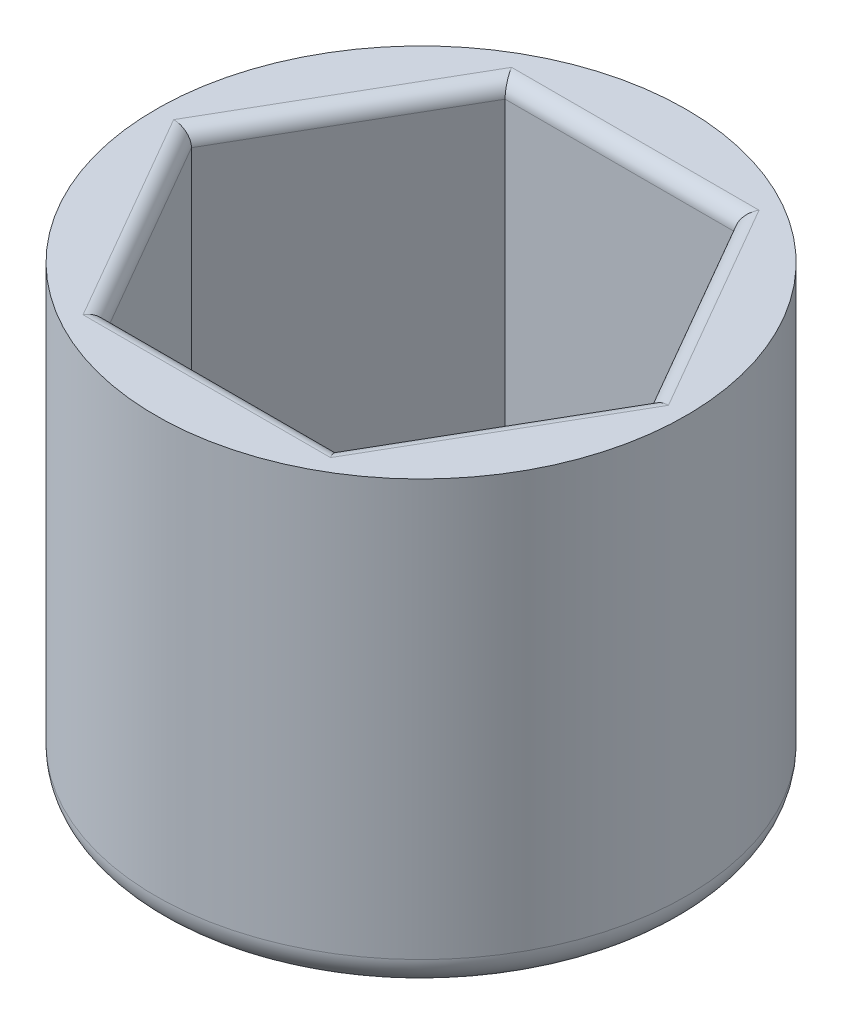
SolidWorks part; units mm, degrees
ref_plane "Alzado" through (0, 0, 0) normal (0, 0, 1) x (1, 0, 0)
ref_plane "Planta" through (0, 0, 0) normal (0, 1, 0) x (1, 0, 0)
ref_plane "Vista lateral" through (0, 0, 0) normal (1, 0, 0) x (0, 0, -1)
sketch "Croquis1" plane through (0, 0, 0) normal (0, 1, 0) x (1, 0, 0)
  line L0 (8.6025, 0) -> (4.3013, 7.45)
  line L1 (-3.7239, 6.45) -> (-7.4478, 0)
  line L2 (-7.4478, 0) -> (-3.7239, -6.45)
  line L3 (-3.7239, -6.45) -> (3.7239, -6.45)
  line L4 (3.7239, -6.45) -> (7.4478, 0)
  line L5 (7.4478, 0) -> (3.7239, 6.45)
  line L6 (3.7239, 6.45) -> (-3.7239, 6.45)
  line L7 (4.3013, 7.45) -> (-4.3013, 7.45)
  line L8 (-4.3013, 7.45) -> (-8.6025, 0)
  line L9 (-8.6025, 0) -> (-4.3013, -7.45)
  line L10 (-4.3013, -7.45) -> (4.3013, -7.45)
  line L11 (4.3013, -7.45) -> (8.6025, 0)
  circle A0 centre (0, 0) radius 6.45 construction
  dimension "D1" = 12.9
  dimension "D2" = 1
extrude "Saliente-Extruir1" add sketch "Croquis1" along normal blind 12
sketch "Croquis2" plane through (0, 0, 0) normal (0, -1, 0) x (1, 0, 0)
  line L6 (8.6025, 0) -> (4.3013, 7.45)
  line L7 (4.3013, 7.45) -> (-4.3013, 7.45)
  line L8 (-4.3013, 7.45) -> (-8.6025, 0)
  line L9 (-8.6025, 0) -> (-4.3013, -7.45)
  line L10 (-4.3013, -7.45) -> (4.3013, -7.45)
  line L11 (4.3013, -7.45) -> (8.6025, 0)
  line L12 (8.6025, 0) -> (4.3013, 7.45)
  line L13 (4.3013, 7.45) -> (-4.3013, 7.45)
  line L14 (-4.3013, 7.45) -> (-8.6025, 0)
  line L15 (-8.6025, 0) -> (-4.3013, -7.45)
  line L16 (-4.3013, -7.45) -> (4.3013, -7.45)
  line L17 (4.3013, -7.45) -> (8.6025, 0)
  dimension "D1" = 0
extrude "Saliente-Extruir2" add sketch "Croquis2" along normal blind 2.5
fillet "Redondeo2" radius 0.5 6 edges at (0, 12, 6.45) (-5.5859, 12, 3.225) (-5.5859, 12, -3.225) (0, 12, -6.45) (5.5859, 12, -3.225) (5.5859, 12, 3.225)
sketch "Croquis3" plane through (0, -2.5, 0) normal (0, -1, 0) x (1, 0, 0)
  line L0 (-4.3013, -7.45) -> (4.3013, -7.45) construction
  line L1 (4.3013, -7.45) -> (8.6025, 0) construction
  line L2 (8.6025, 0) -> (4.3013, 7.45) construction
  line L3 (4.3013, 7.45) -> (-4.3013, 7.45) construction
  line L4 (-4.3013, 7.45) -> (-8.6025, 0) construction
  line L5 (-8.6025, 0) -> (-4.3013, -7.45) construction
  line L6 (-4.3013, -7.45) -> (4.3013, -7.45)
  line L7 (4.3013, -7.45) -> (8.6025, 0)
  line L8 (8.6025, 0) -> (4.3013, 7.45)
  line L9 (4.3013, 7.45) -> (-4.3013, 7.45)
  line L10 (-4.3013, 7.45) -> (-8.6025, 0)
  line L11 (-8.6025, 0) -> (-4.3013, -7.45)
  circle A0 centre (0, 0) radius 8.6025
  line M1 (4.3013, -7.45) -> (8.6025, 0)
  line M2 (8.6025, 0) -> (4.3013, 7.45)
  line M3 (4.3013, 7.45) -> (-4.3013, 7.45)
  line M4 (-4.3013, 7.45) -> (-8.6025, 0)
  line M5 (-8.6025, 0) -> (-4.3013, -7.45)
  line M6 (-4.3013, -7.45) -> (4.3013, -7.45)
extrude "Saliente-Extruir4" add sketch "Croquis3" against normal up to surface (14.5 mm away) contours A0 M2 | A0 M3 | A0 M4 | A0 M5 | A0 M6 | A0 M1 up to face at (0, 12, 0)
fillet "Redondeo5" radius 1 1 edges at (0, -2.5, -8.6025)
